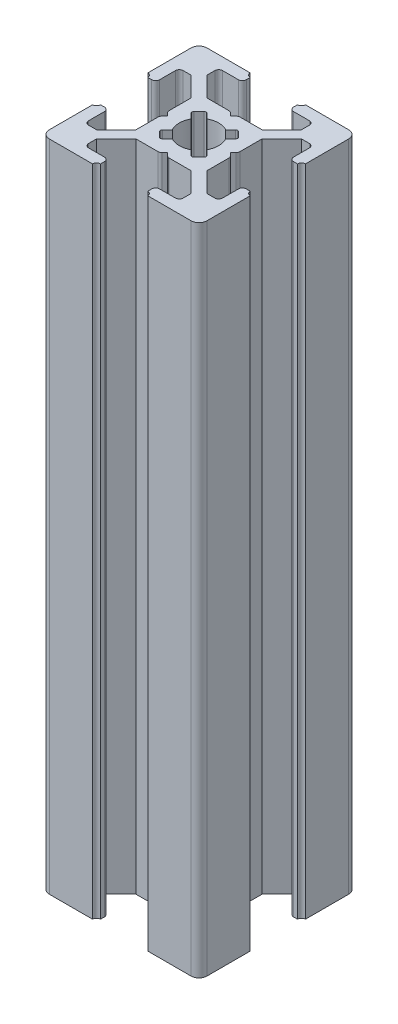
SolidWorks part; units mm, degrees
ref_plane "Front Plane" through (0, 0, 0) normal (0, 0, 1) x (1, 0, 0)
ref_plane "Top Plane" through (0, 0, 0) normal (0, 1, 0) x (1, 0, 0)
ref_plane "Right Plane" through (0, 0, 0) normal (1, 0, 0) x (0, 0, -1)
sketch "Sketch3" plane through (0, 0, 0) normal (0, 1, 0) x (1, 0, 0)
  line L0 (7, 20) -> (7, 18.5)
  line L1 (0, 0) -> (20, 0)
  line L2 (0, 0) -> (0, 20)
  line L3 (0, 20) -> (20, 20)
  line L4 (20, 0) -> (20, 20)
  line L5 (7, 18.5) -> (4, 18.5)
  line L6 (4, 18.5) -> (4, 17)
  line L7 (4, 17) -> (6.5, 14.5)
  line L8 (6.5, 14.5) -> (13.5, 14.5)
  line L9 (13.5, 14.5) -> (16, 17)
  line L10 (16, 17) -> (16, 18.5)
  line L11 (16, 18.5) -> (13, 18.5)
  line L12 (13, 18.5) -> (13, 20)
  line L13 (13, 20) -> (7, 20)
  line L14 (9.5, 14.5) -> (10, 14)
  line L15 (10, 14) -> (10.5, 14.5)
  line L16 (10.5, 14.5) -> (9.5, 14.5)
  line L17 (13, 19.5) -> (13, 20)
  line L18 (13.5, 20) -> (13, 20)
  line L19 (7, 19.5) -> (7, 20)
  line L20 (6.5, 20) -> (7, 20)
  line L21 (0, 13) -> (1.5, 13)
  line L22 (1.5, 13) -> (1.5, 16)
  line L23 (1.5, 16) -> (3, 16)
  line L24 (3, 16) -> (5.5, 13.5)
  line L25 (5.5, 13.5) -> (5.5, 6.5)
  line L26 (5.5, 6.5) -> (3, 4)
  line L27 (3, 4) -> (1.5, 4)
  line L28 (1.5, 4) -> (1.5, 7)
  line L29 (1.5, 7) -> (0, 7)
  line L30 (0, 7) -> (0, 13)
  line L31 (5.5, 10.5) -> (5.5, 9.5)
  line L32 (5.5, 9.5) -> (6, 10)
  line L33 (6, 10) -> (5.5, 10.5)
  line L34 (0.5, 13) -> (0, 13)
  line L35 (0, 13.5) -> (0, 13)
  line L36 (0, 6.5) -> (0, 7)
  line L37 (0.5, 7) -> (0, 7)
  line L38 (10, 20) -> (10, 0) construction
  line L39 (20, 10) -> (0, 10) construction
  line L40 (10, 6) -> (10.5, 5.5)
  line L41 (9.5, 5.5) -> (10, 6)
  line L42 (10.5, 5.5) -> (9.5, 5.5)
  line L43 (13.5, 0) -> (13, 0)
  line L44 (13, 0.5) -> (13, 0)
  line L45 (6.5, 0) -> (7, 0)
  line L46 (7, 0.5) -> (7, 0)
  line L47 (13, 1.5) -> (13, 0)
  line L48 (16, 1.5) -> (13, 1.5)
  line L49 (16, 3) -> (16, 1.5)
  line L50 (13.5, 5.5) -> (16, 3)
  line L51 (6.5, 5.5) -> (13.5, 5.5)
  line L52 (4, 3) -> (6.5, 5.5)
  line L53 (4, 1.5) -> (4, 3)
  line L54 (7, 1.5) -> (4, 1.5)
  line L55 (7, 0) -> (7, 1.5)
  line L56 (13, 0) -> (7, 0)
  line L57 (14.5, 9.5) -> (14, 10)
  line L58 (14.5, 10.5) -> (14.5, 9.5)
  line L59 (14, 10) -> (14.5, 10.5)
  line L60 (19.5, 7) -> (20, 7)
  line L61 (20, 6.5) -> (20, 7)
  line L62 (20, 13.5) -> (20, 13)
  line L63 (19.5, 13) -> (20, 13)
  line L64 (18.5, 7) -> (20, 7)
  line L65 (18.5, 4) -> (18.5, 7)
  line L66 (17, 4) -> (18.5, 4)
  line L67 (14.5, 6.5) -> (17, 4)
  line L68 (14.5, 13.5) -> (14.5, 6.5)
  line L69 (17, 16) -> (14.5, 13.5)
  line L70 (18.5, 16) -> (17, 16)
  line L71 (18.5, 13) -> (18.5, 16)
  line L72 (20, 13) -> (18.5, 13)
  line L73 (20, 7) -> (20, 13)
  arc A0 (13.5, 20) -> (13, 19.5) centre (13, 20) cw
  arc A1 (6.5, 20) -> (7, 19.5) centre (7, 20) ccw
  arc A2 (0.5, 13) -> (0, 13.5) centre (0, 13) ccw
  arc A3 (0.5, 7) -> (0, 6.5) centre (0, 7) cw
  arc A4 (13.5, 0) -> (13, 0.5) centre (13, 0) ccw
  arc A5 (6.5, 0) -> (7, 0.5) centre (7, 0) cw
  arc A6 (19.5, 7) -> (20, 6.5) centre (20, 7) ccw
  arc A7 (19.5, 13) -> (20, 13.5) centre (20, 13) cw
  point P7 (10, 14.5)
  point P16 (10, 20)
  point P26 (5.5, 10)
  point P35 (0, 10)
  dimension "D16" = 0.5
  dimension "D17" = 0.5
  dimension "D28" = 0.5
  dimension "D29" = 0.5
  dimension "D1" = 20
  dimension "D2" = 20
  dimension "D3" = 7
  dimension "D4" = 7
  dimension "D5" = 1.5
  dimension "D6" = 1.5
  dimension "D7" = 3
  dimension "D8" = 3
  dimension "D9" = 1.5
  dimension "D10" = 1.5
  dimension "D11" = 7
  dimension "D12" = 5.5
  dimension "D13" = 0.5
  dimension "D14" = 0.5
  dimension "D15" = 0.5
  dimension "D18" = 7
  dimension "D19" = 7
  dimension "D20" = 1.5
  dimension "D21" = 1.5
  dimension "D22" = 3
  dimension "D23" = 7
  dimension "D24" = 5.5
  dimension "D25" = 0.5
  dimension "D26" = 0.5
  dimension "D27" = 0.5
extrude "Boss-Extrude1" add sketch "Sketch3" along normal blind 83 contours L72 A7 L4 L3 A0 L12 L11 L10 L9 L8 L15 L14 L7 L6 L5 L0 A1 L2 A2 L21 L22 L23 L24 L25 L33 L32 L26 L27 L28 L29 A3 L1 A5 L55 L54 L53 L52 L51 L41 L40 L50 L49 L48 L47 A4
fillet "Fillet1" radius 1 4 edges at (0, 41.5, 0) (20, 41.5, 0) (20, 41.5, -20) (0, 41.5, -20)
sketch "Sketch4" plane through (0, 83, 0) normal (0, 1, 0) x (1, 0, 0)
  line L0 (13.5, 14.5) -> (5.5, 6.5) construction
  line L1 (14.5, 13.5) -> (6.5, 5.5) construction
  line L2 (10.5, 14.5) -> (14.5, 10.5) construction
  line L3 (12, 13) -> (13, 12)
  line L4 (13, 12) -> (8, 7)
  line L5 (8, 7) -> (7, 8)
  line L6 (7, 8) -> (12, 13)
  line L7 (13.5, 14.5) -> (16, 17) construction
  line L8 (17, 16) -> (14.5, 13.5) construction
  line L9 (5.5, 9.5) -> (9.5, 5.5) construction
  line L10 (5.5, 10.5) -> (9.5, 14.5) construction
  line L11 (14.5, 9.5) -> (10.5, 5.5) construction
  line L12 (6.5, 14.5) -> (14.5, 6.5) construction
  line L13 (5.5, 13.5) -> (13.5, 5.5) construction
  line L14 (7, 12) -> (8, 13)
  line L15 (8, 13) -> (13, 8)
  line L16 (13, 8) -> (12, 7)
  line L17 (12, 7) -> (7, 12)
  line L18 (4, 17) -> (6.5, 14.5) construction
  line L19 (3, 16) -> (5.5, 13.5) construction
  line L20 (20, 10) -> (0, 10) construction
  circle A0 centre (10, 10) radius 2.5
  dimension "D1" = 5
extrude "Cut-Extrude1" cut sketch "Sketch4" against normal through all contours L6 A0 L15 | L4 A0 L6 L15 | L15 A0 L17 L6 | L17 L4 L15 L6 | L17 A0 L6 | L6 A0 L4 L17 | L4 A0 L17 | L17 A0 L15 L4 | L15 A0 L4 | A0 L6 L5 L4 | A0 L17 L16 L15 | A0 L4 L3 L6 | A0 L15 L14 L17
fillet "Fillet2" radius 0.5 24 edges at (1.5, 41.5, -16) (1.5, 41.5, -13) (5.5, 41.5, -10.5) (5.5, 41.5, -9.5) (1.5, 41.5, -7) (1.5, 41.5, -4) (4, 41.5, -1.5) (7, 41.5, -1.5) (9.5, 41.5, -5.5) (10.5, 41.5, -5.5) (13, 41.5, -1.5) (16, 41.5, -1.5) (18.5, 41.5, -4) (18.5, 41.5, -7) (18.5, 41.5, -13) (18.5, 41.5, -16) (14.5, 41.5, -9.5) (14.5, 41.5, -10.5) (10.5, 41.5, -14.5) (9.5, 41.5, -14.5) (16, 41.5, -18.5) (13, 41.5, -18.5) (7, 41.5, -18.5) (4, 41.5, -18.5)
fillet "Fillet3" radius 0.25 8 edges at (13, 41.5, -8) (12, 41.5, -7) (13, 41.5, -12) (12, 41.5, -13) (8, 41.5, -13) (7, 41.5, -12) (7, 41.5, -8) (8, 41.5, -7)
